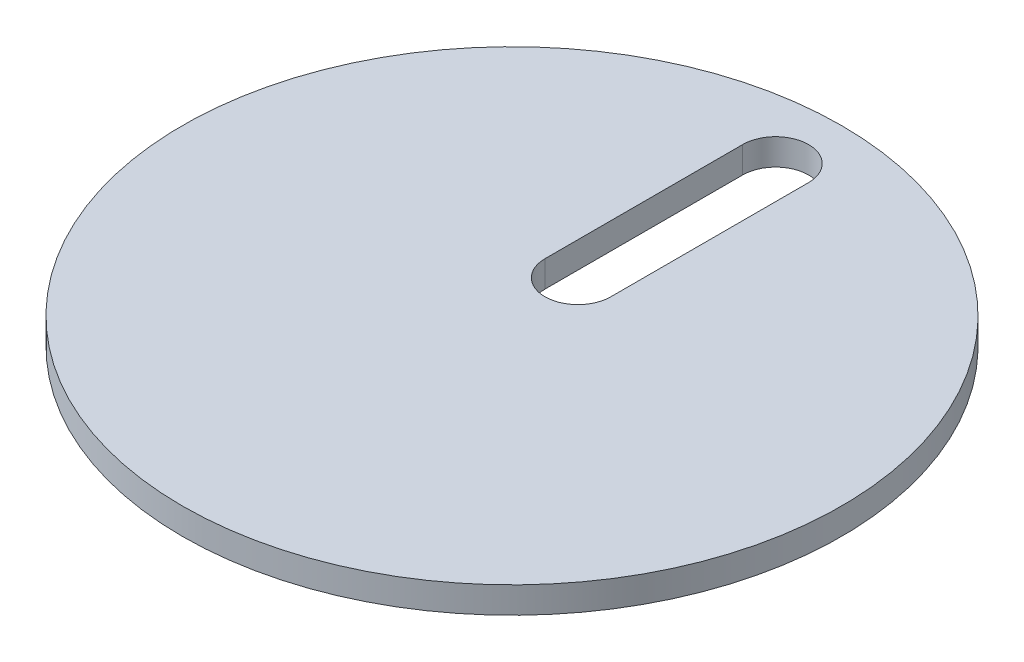
SolidWorks part; units mm, degrees
ref_plane "Front Plane" through (0, 0, 0) normal (0, 0, 1) x (1, 0, 0)
ref_plane "Top Plane" through (0, 0, 0) normal (0, 1, 0) x (1, 0, 0)
ref_plane "Right Plane" through (0, 0, 0) normal (1, 0, 0) x (0, 0, -1)
sketch "Sketch1" plane through (0, 0, 0) normal (0, 1, 0) x (1, 0, 0)
  line L0 (0.1074, 17.2431) -> (0.1074, 47.2431) construction
  line L1 (-4.8926, 17.2431) -> (-4.8926, 47.2431)
  line L2 (5.1074, 17.2431) -> (5.1074, 47.2431)
  circle A0 centre (0.1074, 7.2431) radius 50
  arc A1 (-4.8926, 17.2431) -> (5.1074, 17.2431) centre (0.1074, 17.2431) ccw
  arc A2 (5.1074, 47.2431) -> (-4.8926, 47.2431) centre (0.1074, 47.2431) ccw
  point P4 (0.1074, 32.2431)
  point P9 (0, 0)
  dimension "D1" = 100
  dimension "D3" = 5
  dimension "D2" = 30
  dimension "D4" = 40
extrude "Boss-Extrude1" add sketch "Sketch1" along normal blind 4
